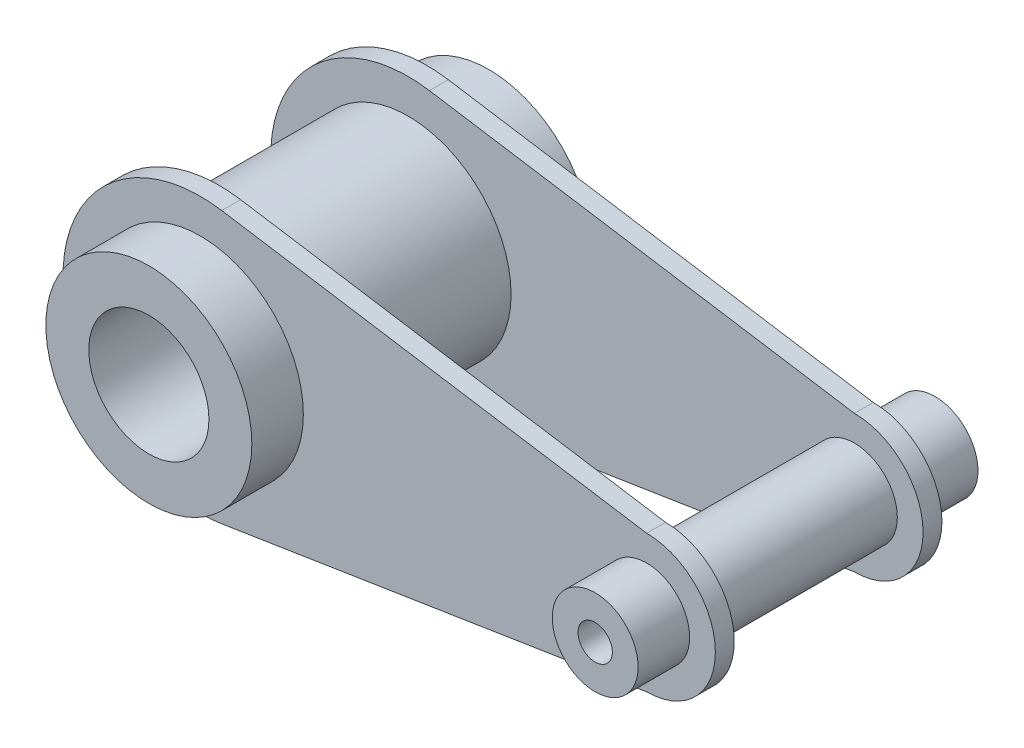
SolidWorks part; units mm, degrees
ref_plane "Front Plane" through (0, 0, 0) normal (0, 0, 1) x (1, 0, 0)
ref_plane "Top Plane" through (0, 0, 0) normal (0, 1, 0) x (1, 0, 0)
ref_plane "Right Plane" through (0, 0, 0) normal (1, 0, 0) x (0, 0, -1)
sketch "Sketch1" plane through (0, 0, 0) normal (0, 0, 1) x (1, 0, 0)
  line L0 (6.2289, 39.512) -> (130, 20)
  line L1 (6.2289, -39.512) -> (130, -20)
  arc A0 (6.2289, 39.512) -> (6.2289, -39.512) centre (0, 0) ccw
  arc A1 (130, -20) -> (130, 20) centre (130, 0) ccw
  dimension "D1" = 80
  dimension "D2" = 40
  dimension "D3" = 130
extrude "Boss-Extrude1" add sketch "Sketch1" along normal blind 5.5
ref_plane "Plane3" through (0, 0, 20.5) normal (0, 0, 1) x (1, 0, 0)
sketch "Sketch2" plane through (0, 0, 20.5) normal (0, 0, 1) x (1, 0, 0)
  circle A0 centre (0, 0) radius 30
  circle A1 centre (0, 0) radius 17.5
  circle A2 centre (130, 0) radius 12.5
  circle A3 centre (130, 0) radius 5
  dimension "D1" = 60
  dimension "D2" = 35
  dimension "D3" = 25
  dimension "D4" = 10
extrude "Boss-Extrude2" add sketch "Sketch2" against normal blind 99
sketch "Sketch3" plane through (0, 0, 5.5) normal (0, 0, 1) x (1, 0, 0)
  circle A1 centre (0, 0) radius 17.5
  circle A2 centre (0, 0) radius 17.5
  circle A3 centre (130, 0) radius 5
  circle A4 centre (130, 0) radius 5
  dimension "D1" = 0
  dimension "D2" = 0
extrude "Cut-Extrude1" cut sketch "Sketch3" against normal blind 99
ref_plane "Plane4" through (0, 0, -27.5) normal (0, 0, 1) x (1, 0, 0)
mirror "Mirror5" about plane through (0, 0, -27.5) normal (0, 0, 1) of "Boss-Extrude1"
sketch "Sketch4" plane through (0, 0, -60.5) normal (0, 0, -1) x (-1, 0, 0)
  circle A0 centre (0, 0) radius 17.5
  circle A1 centre (-130, 0) radius 5
extrude "Cut-Extrude2" cut sketch "Sketch4" against normal blind 99 contours A1
sketch "Sketch5" plane through (0, 0, -60.5) normal (0, 0, -1) x (-1, 0, 0)
  circle A1 centre (0, 0) radius 17.5
  circle A2 centre (0, 0) radius 17.5
  dimension "D1" = 0
extrude "Cut-Extrude3" cut sketch "Sketch5" against normal blind 99
